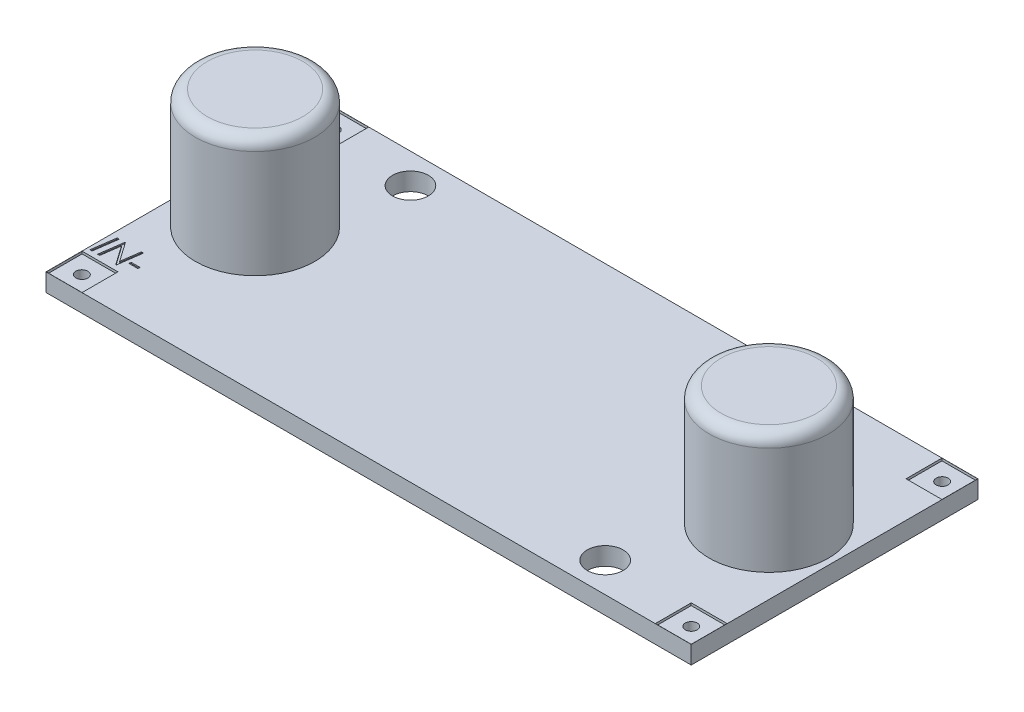
SolidWorks part; units mm, degrees
ref_plane "Front Plane" through (0, 0, 0) normal (0, 0, 1) x (1, 0, 0)
ref_plane "Top Plane" through (0, 0, 0) normal (0, 1, 0) x (1, 0, 0)
ref_plane "Right Plane" through (0, 0, 0) normal (1, 0, 0) x (0, 0, -1)
sketch "Sketch1" plane through (0, 0, 0) normal (0, 1, 0) x (1, 0, 0)
  line L1 (0, 0) -> (54, 0)
  line L2 (0, 0) -> (0, -24)
  line L3 (0, -24) -> (54, -24)
  line L4 (54, 0) -> (54, -24)
  dimension "D1" = 54
  dimension "D2" = 24
extrude "Boss-Extrude1" add sketch "Sketch1" along normal blind 1.5
sketch "Sketch2" plane through (0, 1.5, 0) normal (0, 1, 0) x (1, 0, 0)
  line L0 (0, 0) -> (0, -24) construction
  line L1 (54, 0) -> (0, 0) construction
  line L2 (54, -24) -> (54, 0) construction
  line L3 (0, -24) -> (54, -24) construction
  circle A0 centre (9, -2.5) radius 1.5
  circle A1 centre (44.3, -21.5) radius 1.5
  dimension "D1" = 3
  dimension "D4" = 3
  dimension "D5" = 9.7
  dimension "D6" = 2.5
  dimension "D2" = 9
  dimension "D3" = 2.5
extrude "Cut-Extrude1" cut sketch "Sketch2" against normal up to next
sketch "Sketch4" plane through (0, 1.5, 0) normal (0, 1, 0) x (1, 0, 0)
  line L0 (54, 0) -> (0, 0) construction
  line L1 (0.01, -0.01) -> (3.01, -0.01)
  line L2 (0.01, -0.01) -> (0.01, -3.01)
  line L3 (0.01, -3.01) -> (3.01, -3.01)
  line L4 (3.01, -0.01) -> (3.01, -3.01)
  line L5 (0, 0) -> (0, -24) construction
  line L6 (27, 0) -> (27, -24) construction
  line L7 (0, -24) -> (54, -24) construction
  line L8 (0, -12) -> (54, -12) construction
  line L9 (54, -24) -> (54, 0) construction
  line L10 (53.99, -0.01) -> (53.99, -3.01)
  line L11 (53.99, -0.01) -> (50.99, -0.01)
  line L12 (53.99, -3.01) -> (50.99, -3.01)
  line L13 (50.99, -0.01) -> (50.99, -3.01)
  line L14 (0.01, -23.99) -> (0.01, -20.99)
  line L15 (0.01, -23.99) -> (3.01, -23.99)
  line L16 (3.01, -23.99) -> (3.01, -20.99)
  line L17 (0.01, -20.99) -> (3.01, -20.99)
  line L18 (53.99, -23.99) -> (50.99, -23.99)
  line L19 (53.99, -23.99) -> (53.99, -20.99)
  line L20 (50.99, -23.99) -> (50.99, -20.99)
  line L21 (53.99, -20.99) -> (50.99, -20.99)
  dimension "D1" = 3
  dimension "D2" = 3
  dimension "D3" = 0.01
  dimension "D4" = 0.01
extrude "Cut-Extrude2" cut sketch "Sketch4" against normal blind 0.2
sketch "Sketch5" plane through (0, 0, 0) normal (0, -1, 0) x (1, 0, 0)
  line L0 (54, 0) -> (0, 0) construction
  line L1 (54, 24) -> (54, 0) construction
  line L2 (27, 0) -> (27, 24) construction
  line L3 (0, 24) -> (54, 24) construction
  line L4 (0, 12) -> (54, 12) construction
  line L5 (0, 0) -> (0, 24) construction
  circle A0 centre (52.5, 1.5) radius 0.5
  circle A1 centre (52.5, 22.5) radius 0.5
  circle A2 centre (1.5, 1.5) radius 0.5
  circle A3 centre (1.5, 22.5) radius 0.5
  dimension "D1" = 1
  dimension "D2" = 1.5
  dimension "D3" = 1.5
extrude "Cut-Extrude3" cut sketch "Sketch5" against normal up to next
sketch "Sketch8" plane through (0, 1.5, 0) normal (0, 1, 0) x (1, 0, 0)
  text T0 "<i>IN+</i>" font "Century Gothic" height 2
extrude "Cut-Extrude4" cut sketch "Sketch8" against normal blind 0.1
sketch "Sketch9" plane through (0, 1.5, 0) normal (0, 1, 0) x (1, 0, 0)
  text T0 "<i>IN-</i>" font "Century Gothic" height 2
extrude "Cut-Extrude5" cut sketch "Sketch9" against normal blind 0.1
sketch "Sketch10" plane through (0, 1.5, 0) normal (0, 1, 0) x (1, 0, 0)
  line L0 (0, 0) -> (0, -24) construction
  line L1 (54, 0) -> (0, 0) construction
  line L2 (27, 0) -> (27, -24) construction
  line L3 (0, -24) -> (54, -24) construction
  circle A0 centre (5.5, -12) radius 5
  circle A1 centre (48.5, -12) radius 5
  dimension "D1" = 10
  dimension "D2" = 5.5
  dimension "D3" = 12
extrude "Boss-Extrude2" add sketch "Sketch10" along normal blind 10
fillet "Fillet1" radius 1 2 edges at (5.5, 11.5, 17) (48.5, 11.5, 7)
